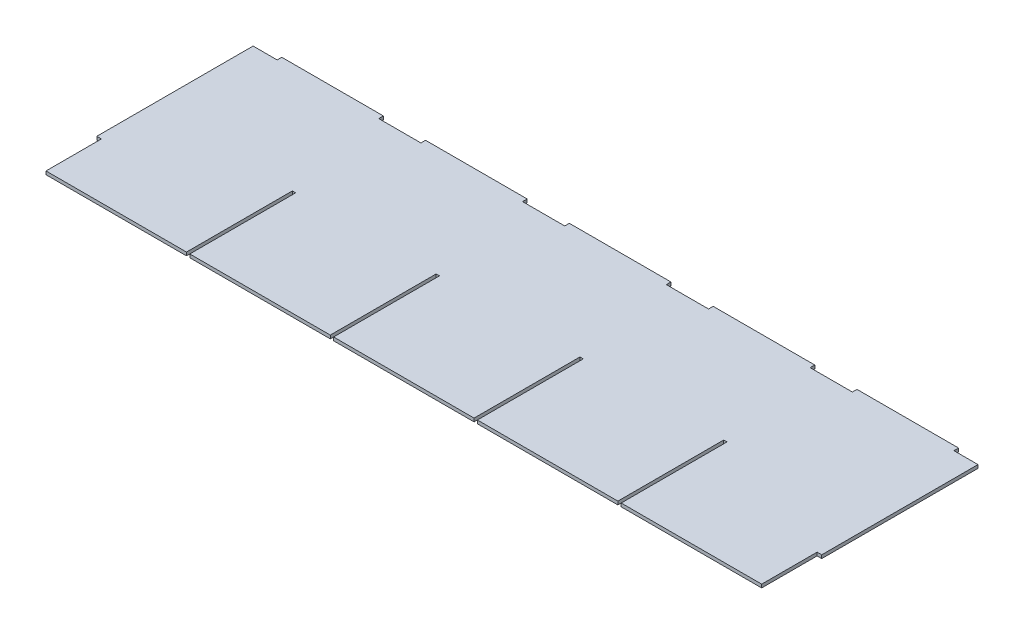
SolidWorks part; units mm, degrees
material "6061-T6 (SS)"
ref_plane "X-Y Datum" through (0, 0, 0) normal (0, 0, 1) x (1, 0, 0)
ref_plane "X-Z Datum" through (0, 0, 0) normal (0, 1, 0) x (1, 0, 0)
ref_plane "Y-Z Datum" through (0, 0, 0) normal (1, 0, 0) x (0, 0, -1)
sketch "Sketch1" plane through (0, 0, 0) normal (0, 1, 0) x (1, 0, 0)
  line L1 (-249.174, 72.771) -> (249.174, 72.771)
  line L2 (-249.174, 72.771) -> (-249.174, -72.771)
  line L3 (-249.174, -72.771) -> (249.174, -72.771)
  line L4 (249.174, 72.771) -> (249.174, -72.771)
  line L5 (-249.174, 72.771) -> (249.174, -72.771) construction
  line L6 (-249.174, -72.771) -> (249.174, 72.771) construction
  point P0 (0, 0)
  dimension "D1" = 498.348
  dimension "D2" = 145.542
extrude "Boss-Extrude1" add sketch "Sketch1" along normal mid plane 2.286
sketch "Sketch2" plane through (0, 0, -72.771) normal (0, 0, -1) x (-1, 0, 0)
  line L24 (-232.6386, -1.143) -> (-232.6386, 1.143)
  line L25 (-232.6386, 1.143) -> (-162.7886, 1.143)
  line L26 (-162.7886, -1.143) -> (-232.6386, -1.143)
  line L27 (-162.7886, 1.143) -> (-162.7886, -1.143)
extrude "Boss-Extrude2" add sketch "Sketch2" along normal blind 3.175
pattern_linear "LPattern1" count 5 spacing 98.8568 along (-1, 0, 0) of "Boss-Extrude2"
sketch "Sketch3" plane through (0, -1.143, 0) normal (0, -1, 0) x (1, 0, 0)
  line L0 (-249.174, 72.771) -> (249.174, 72.771) construction
  line L1 (-249.174, 72.771) -> (249.174, 72.771)
  line L2 (-249.174, -72.771) -> (-249.174, 72.771) construction
  line L3 (-249.174, 72.771) -> (-245.999, 72.771)
  line L4 (-249.174, 72.771) -> (-249.174, 34.671)
  line L5 (-249.174, 34.671) -> (-245.999, 34.671)
  line L6 (-245.999, 72.771) -> (-245.999, 34.671)
  line L7 (-249.174, -72.771) -> (-249.174, 72.771)
  line M6 (-249.174, 72.771) -> (-249.174, -72.771)
  dimension "D1" = 3.175
  dimension "D2" = 145.542
  dimension "D3" = 38.1
extrude "Cut-Extrude1" cut sketch "Sketch3" against normal through all contours L6 L1 L5 M6
mirror "Mirror2" about plane through (0, 0, 0) normal (1, 0, 0) of "Cut-Extrude1"
sketch "Sketch5" plane through (0, -1.143, 0) normal (0, -1, 0) x (1, 0, 0)
  line L0 (-245.999, 72.771) -> (245.999, 72.771) construction
  line L1 (-245.999, 72.771) -> (245.999, 72.771)
  line L2 (-149.4282, 34.671) -> (-149.4282, -72.771) construction
  line L3 (-149.4282, 72.771) -> (-149.4282, -72.771)
  line L5 (-149.4282, 72.771) -> (-147.1422, 72.771)
  line L6 (-149.4282, 72.771) -> (-149.4282, 0)
  line L7 (-149.4282, 0) -> (-147.1422, 0)
  line L8 (-147.1422, 72.771) -> (-147.1422, 0)
  dimension "D1" = 2.286
  dimension "D2" = 72.771
extrude "Cut-Extrude2" cut sketch "Sketch5" against normal through all contours L8 L1 L3 L7
pattern_linear "LPattern2" count 4 spacing 98.8568 along (1, 0, 0) of "Cut-Extrude2"
